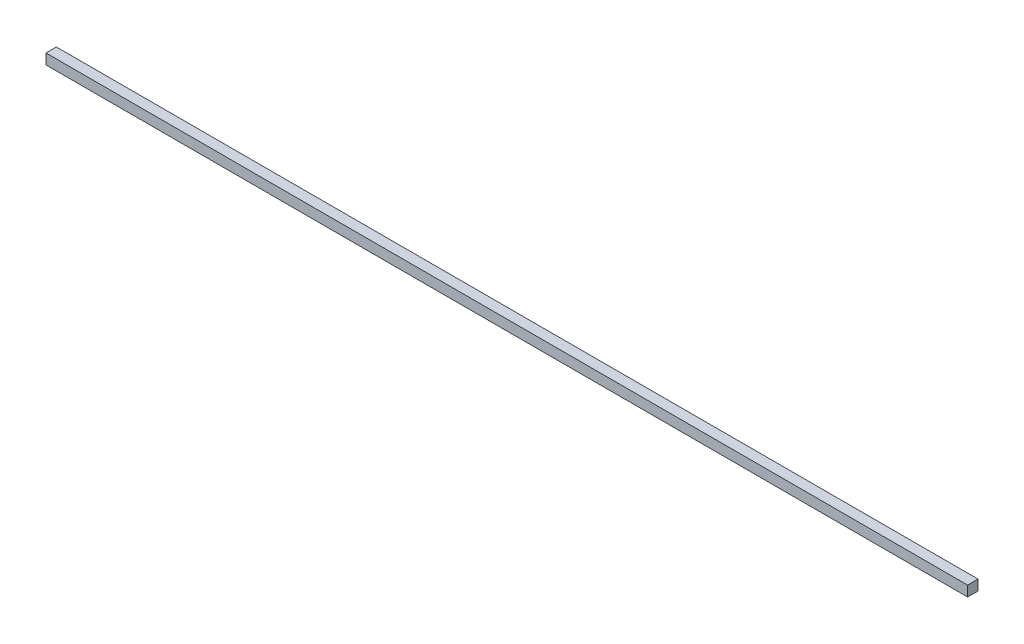
SolidWorks part; units mm, degrees
ref_plane "Front Plane" through (0, 0, 0) normal (0, 0, 1) x (1, 0, 0)
ref_plane "Top Plane" through (0, 0, 0) normal (0, 1, 0) x (1, 0, 0)
ref_plane "Right Plane" through (0, 0, 0) normal (1, 0, 0) x (0, 0, -1)
sketch "Sketch1" plane through (0, 0, 0) normal (0, 1, 0) x (1, 0, 0)
  line L0 (-444.265, 5) -> (444.265, -5) construction
  line L1 (-444.265, 5) -> (444.265, 5)
  line L2 (-444.265, 5) -> (-444.265, -5)
  line L3 (-444.265, -5) -> (444.265, -5)
  line L4 (444.265, 5) -> (444.265, -5)
  dimension "D1" = 888.53
  dimension "D2" = 10
extrude "Boss-Extrude1" add sketch "Sketch1" along normal blind 10
